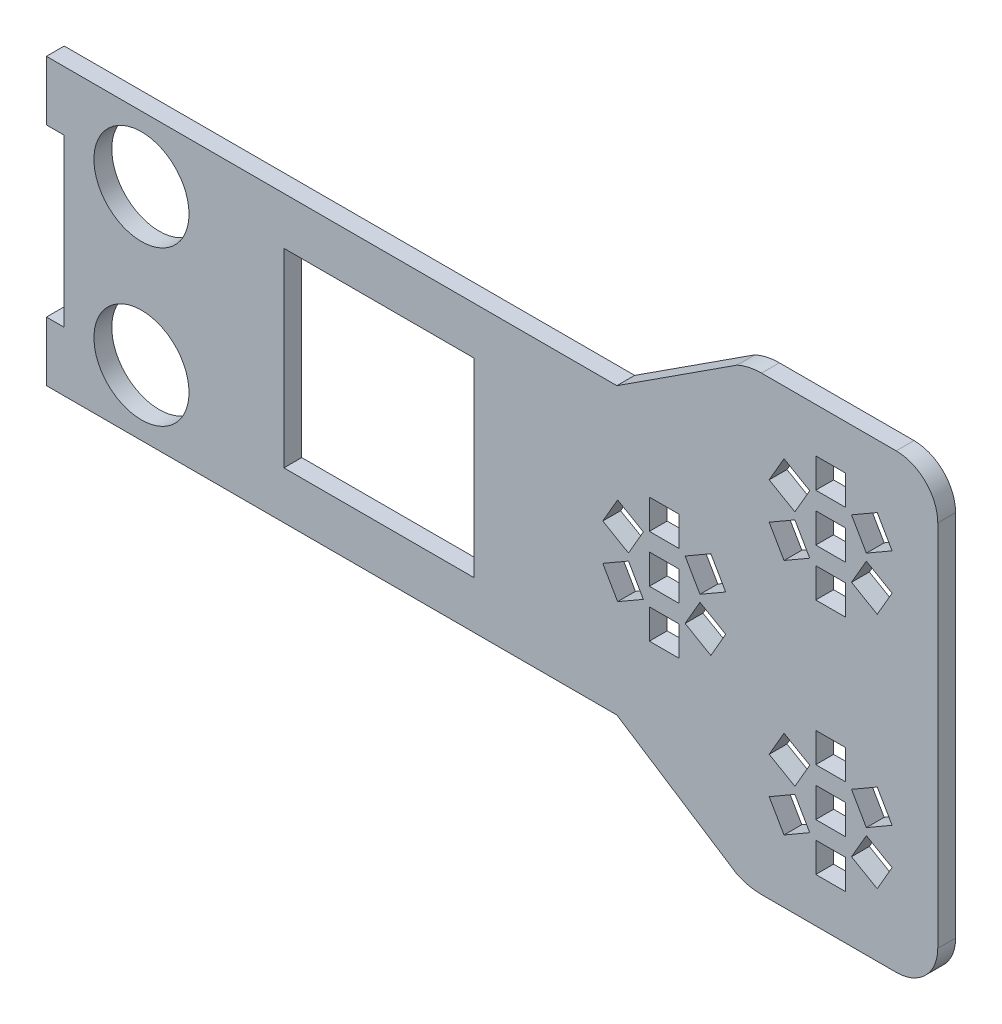
SolidWorks part; units mm, degrees
ref_plane "Alzado" through (0, 0, 0) normal (0, 0, 1) x (1, 0, 0)
ref_plane "Planta" through (0, 0, 0) normal (0, 1, 0) x (1, 0, 0)
ref_plane "Vista lateral" through (0, 0, 0) normal (1, 0, 0) x (0, 0, -1)
sketch "Model" plane through (0, 0, 0) normal (0, 0, 1) x (1, 0, 0)
  line L0 (11.144, 41.7484) -> (-20.856, 41.7484)
  line L1 (11.144, 9.7484) -> (11.144, 41.7484)
  line L2 (-20.856, 9.7484) -> (11.144, 9.7484)
  line L3 (-20.856, 41.7484) -> (-20.856, 9.7484)
  line L4 (-57.8247, 11.7484) -> (-57.8247, 39.7484)
  line L5 (-60.8247, 49.7484) -> (35.1753, 49.7484)
  line L6 (-60.8247, 1.7484) -> (-60.8247, 11.7484)
  line L7 (-60.8247, 11.7484) -> (-57.8247, 11.7484)
  line L8 (-60.8247, 49.7484) -> (-60.8247, 39.7484)
  line L9 (-60.8247, 39.7484) -> (-57.8247, 39.7484)
  line L10 (65.1308, 45.1634) -> (67.6308, 40.8333)
  line L11 (65.1308, 5.1634) -> (67.6308, 0.8333)
  line L12 (37.1308, 25.1634) -> (39.6308, 20.8333)
  line L13 (60.8007, 42.6634) -> (65.1308, 45.1634)
  line L14 (60.8007, 2.6634) -> (65.1308, 5.1634)
  line L15 (32.8007, 22.6634) -> (37.1308, 25.1634)
  line L16 (63.3007, 38.3333) -> (60.8007, 42.6634)
  line L17 (63.3007, -1.6667) -> (60.8007, 2.6634)
  line L18 (35.3007, 18.3333) -> (32.8007, 22.6634)
  line L19 (67.6308, 40.8333) -> (63.3007, 38.3333)
  line L20 (67.6308, 0.8333) -> (63.3007, -1.6667)
  line L21 (39.6308, 20.8333) -> (35.3007, 18.3333)
  line L22 (60.8007, 48.8333) -> (63.3007, 53.1634)
  line L23 (60.8007, 8.8333) -> (63.3007, 13.1634)
  line L24 (32.8007, 28.8333) -> (35.3007, 33.1634)
  line L25 (65.1308, 46.3333) -> (60.8007, 48.8333)
  line L26 (65.1308, 6.3333) -> (60.8007, 8.8333)
  line L27 (37.1308, 26.3333) -> (32.8007, 28.8333)
  line L28 (67.6308, 50.6634) -> (65.1308, 46.3333)
  line L29 (67.6308, 10.6634) -> (65.1308, 6.3333)
  line L30 (39.6308, 30.6634) -> (37.1308, 26.3333)
  line L31 (63.3007, 53.1634) -> (67.6308, 50.6634)
  line L32 (63.3007, 13.1634) -> (67.6308, 10.6634)
  line L33 (35.3007, 33.1634) -> (39.6308, 30.6634)
  line L34 (73.644, 35.2484) -> (68.644, 35.2484)
  line L35 (73.644, -4.7516) -> (68.644, -4.7516)
  line L36 (45.644, 15.2484) -> (40.644, 15.2484)
  line L37 (73.644, 40.2484) -> (73.644, 35.2484)
  line L38 (73.644, 0.2484) -> (73.644, -4.7516)
  line L39 (45.644, 20.2484) -> (45.644, 15.2484)
  line L40 (68.644, 40.2484) -> (73.644, 40.2484)
  line L41 (68.644, 0.2484) -> (73.644, 0.2484)
  line L42 (40.644, 20.2484) -> (45.644, 20.2484)
  line L43 (68.644, 35.2484) -> (68.644, 40.2484)
  line L44 (68.644, -4.7516) -> (68.644, 0.2484)
  line L45 (40.644, 15.2484) -> (40.644, 20.2484)
  line L46 (77.1571, 46.3333) -> (74.6571, 50.6634)
  line L47 (77.1571, 6.3333) -> (74.6571, 10.6634)
  line L48 (49.1571, 26.3333) -> (46.6571, 30.6634)
  line L49 (81.4872, 48.8333) -> (77.1571, 46.3333)
  line L50 (81.4872, 8.8333) -> (77.1571, 6.3333)
  line L51 (53.4872, 28.8333) -> (49.1571, 26.3333)
  line L52 (78.9872, 53.1634) -> (81.4872, 48.8333)
  line L53 (78.9872, 13.1634) -> (81.4872, 8.8333)
  line L54 (50.9872, 33.1634) -> (53.4872, 28.8333)
  line L55 (74.6571, 50.6634) -> (78.9872, 53.1634)
  line L56 (74.6571, 10.6634) -> (78.9872, 13.1634)
  line L57 (46.6571, 30.6634) -> (50.9872, 33.1634)
  line L58 (81.4872, 42.6634) -> (78.9872, 38.3333)
  line L59 (81.4872, 2.6634) -> (78.9872, -1.6667)
  line L60 (53.4872, 22.6634) -> (50.9872, 18.3333)
  line L61 (77.1571, 5.1634) -> (81.4872, 2.6634)
  line L62 (49.1571, 25.1634) -> (53.4872, 22.6634)
  line L63 (77.1571, 45.1634) -> (81.4872, 42.6634)
  line L64 (74.6571, 0.8333) -> (77.1571, 5.1634)
  line L65 (46.6571, 20.8333) -> (49.1571, 25.1634)
  line L66 (74.6571, 40.8333) -> (77.1571, 45.1634)
  line L67 (78.9872, -1.6667) -> (74.6571, 0.8333)
  line L68 (50.9872, 18.3333) -> (46.6571, 20.8333)
  line L69 (78.9872, 38.3333) -> (74.6571, 40.8333)
  line L70 (73.644, 11.2484) -> (68.644, 11.2484)
  line L71 (45.644, 31.2484) -> (40.644, 31.2484)
  line L72 (73.644, 51.2484) -> (68.644, 51.2484)
  line L73 (73.644, 16.2484) -> (73.644, 11.2484)
  line L74 (45.644, 36.2484) -> (45.644, 31.2484)
  line L75 (73.644, 56.2484) -> (73.644, 51.2484)
  line L76 (68.644, 16.2484) -> (73.644, 16.2484)
  line L77 (40.644, 36.2484) -> (45.644, 36.2484)
  line L78 (68.644, 56.2484) -> (73.644, 56.2484)
  line L79 (68.644, 11.2484) -> (68.644, 16.2484)
  line L80 (40.644, 31.2484) -> (40.644, 36.2484)
  line L81 (68.644, 51.2484) -> (68.644, 56.2484)
  line L82 (73.644, 3.2484) -> (68.644, 3.2484)
  line L83 (45.644, 23.2484) -> (40.644, 23.2484)
  line L84 (73.644, 43.2484) -> (68.644, 43.2484)
  line L85 (73.644, 8.2484) -> (73.644, 3.2484)
  line L86 (45.644, 28.2484) -> (45.644, 23.2484)
  line L87 (73.644, 48.2484) -> (73.644, 43.2484)
  line L88 (68.644, 8.2484) -> (73.644, 8.2484)
  line L89 (40.644, 28.2484) -> (45.644, 28.2484)
  line L90 (68.644, 48.2484) -> (73.644, 48.2484)
  line L91 (68.644, 3.2484) -> (68.644, 8.2484)
  line L92 (40.644, 23.2484) -> (40.644, 28.2484)
  line L93 (68.644, 43.2484) -> (68.644, 48.2484)
  line L94 (82.1753, -12.2516) -> (59.5165, -12.2516)
  line L95 (59.5165, 63.7484) -> (82.1753, 63.7484)
  line L96 (89.1753, 56.7484) -> (89.1753, -5.2516)
  line L97 (55.432, 62.8761) -> (35.1753, 49.7484)
  line L98 (55.432, -11.3794) -> (35.1753, 1.7484)
  line L99 (35.1753, 1.7484) -> (-60.8247, 1.7484)
  circle A0 centre (-44.8247, 12.7484) radius 8
  circle A1 centre (-44.8247, 38.7484) radius 8
  arc A2 (89.1753, 56.7484) -> (82.1753, 63.7484) centre (82.1753, 56.7484) ccw
  arc A3 (82.1753, -12.2516) -> (89.1753, -5.2516) centre (82.1753, -5.2516) ccw
  arc A4 (59.5165, 63.7484) -> (55.432, 62.8761) centre (59.5165, 53.7484) ccw
  arc A5 (55.432, -11.3794) -> (59.5165, -12.2516) centre (59.5165, -2.2516) ccw
extrude "Saliente-Extruir1" add sketch "Model" along normal blind 3
